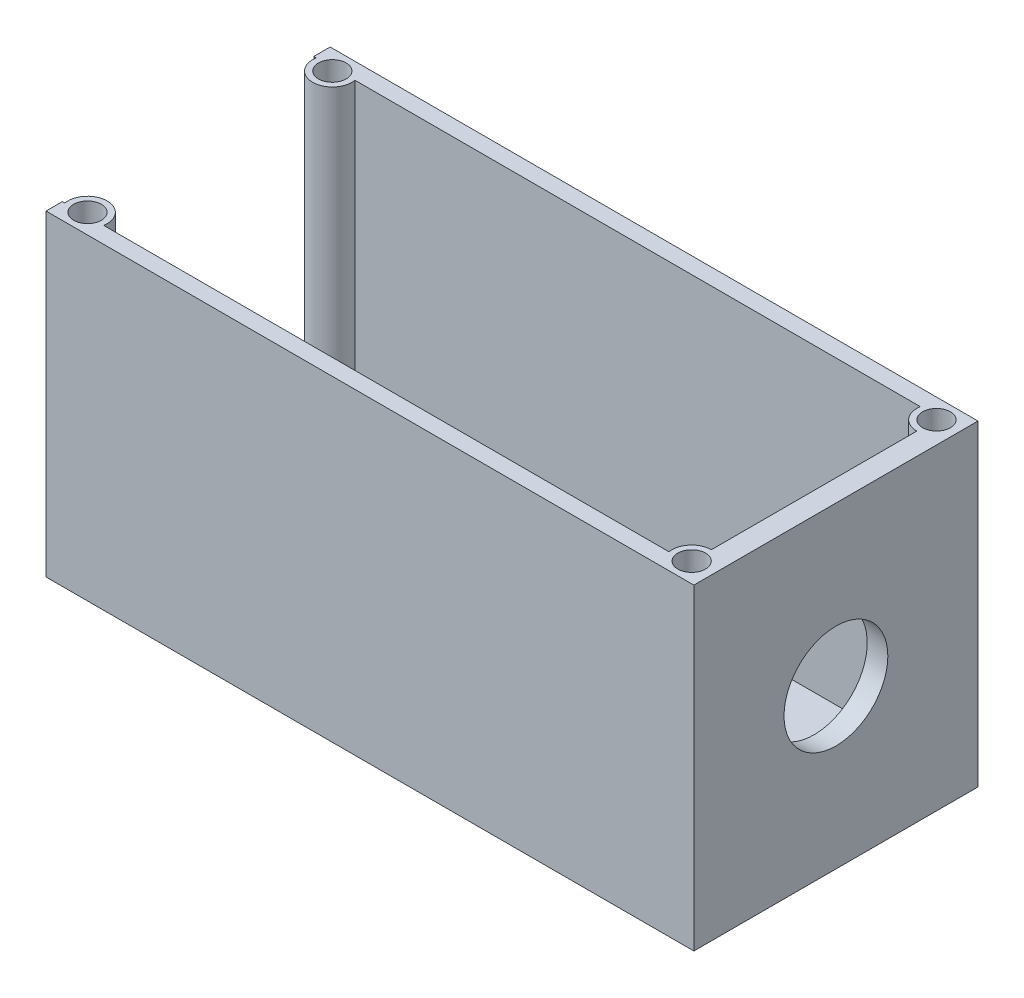
SolidWorks part; units mm, degrees
ref_plane "Front Plane" through (0, 0, 0) normal (0, 0, 1) x (1, 0, 0)
ref_plane "Top Plane" through (0, 0, 0) normal (0, 1, 0) x (1, 0, 0)
ref_plane "Right Plane" through (0, 0, 0) normal (1, 0, 0) x (0, 0, -1)
sketch "Sketch1" plane through (0, 0, 0) normal (0, 1, 0) x (1, 0, 0)
  line L1 (0, 0) -> (59.28, 0)
  line L2 (0, 0) -> (0, 26)
  line L3 (0, 26) -> (59.28, 26)
  line L4 (59.28, 0) -> (59.28, 26)
  dimension "D1" = 59.28
  dimension "D2" = 26
extrude "Boss-Extrude2" add sketch "Sketch1" along normal blind 29 contours L2 L3 L4 L1
sketch "Sketch3" plane through (0, 29, 0) normal (0, 1, 0) x (1, 0, 0)
  line L0 (0, 0) -> (0, 26) construction
  line L1 (57.28, 1.5) -> (0, 1.5)
  line L2 (57.28, 1.5) -> (57.28, 24.5)
  line L3 (57.28, 24.5) -> (0, 24.5)
  line L4 (0, 1.5) -> (0, 24.5)
  line L5 (0, 26) -> (59.28, 26) construction
  line L6 (0, 0) -> (59.28, 0) construction
  line L7 (59.28, 0) -> (59.28, 26) construction
  dimension "D1" = 1.5
  dimension "D2" = 1.5
  dimension "D3" = 2
extrude "Cut-Extrude1" cut sketch "Sketch3" against normal offset from surface (27.5 mm away) 1.5 up to face at (29.64, 0, -13)
sketch "Sketch4" plane through (59.28, 0, 0) normal (1, 0, 0) x (0, 0, -1)
  line L0 (0, 29) -> (26, 0) construction
  line L2 (26, 29) -> (0, 0) construction
  circle A0 centre (13, 14.5) radius 4.75
  point P6 (13, 14.5)
sketch "Sketch5" plane through (57.28, 0, 0) normal (-1, 0, 0) x (0, 0, 1)
  line L0 (-26, 29) -> (0, 0) construction
  line L2 (0, 29) -> (-26, 0) construction
  circle A0 centre (-13, 14.5) radius 4.8654
loft "Cut-Loft1" cut profiles "Sketch4", "Sketch5"
sketch "Sketch9" plane through (0, 29, 0) normal (0, 1, 0) x (1, 0, 0)
  line L0 (0, 0) -> (59.28, 0) construction
  line L2 (57.28, 1.5) -> (57.28, 24.5) construction
  circle A1 centre (57.28, 1.8) radius 1.8
  point P5 (0, 0)
extrude "Boss-Extrude4" add sketch "Sketch9" against normal up to surface (27.5 mm away) up to face at (28.64, 1.5, -13)
hole_wizard "Ø2.0mm Dowel Hole3" positions "Sketch12" profile "Sketch13" hole size "Ø2.0" standard "ANSI Metric"
sketch "Sketch12" plane through (0, 29, 0) normal (0, 1, 0) x (1, 0, 0)
  arc A0 (57.28, 3.6) -> (55.5052, 1.5) centre (57.28, 1.8) ccw construction
  point P0 (57.28, 1.8)
  dimension "D1" = 0
sketch "Sketch13" plane through (57.28, 29, -1.8) normal (1, 0, 0) x (0, 0, 1)
  line L0 (0, 0) -> (0, 10)
  line L1 (0, 10) -> (1.27, 10)
  line L2 (1.27, 10) -> (1.27, 0)
  line L5 (1.27, 0) -> (0, 0)
  line L10 (0, 10) -> (-1.27, 10) construction
  line L11 (0, -6.35) -> (0, 107.95) construction
  dimension "Hole Dia." = 2.54
  dimension "Hole Depth" = 10
  dimension "Drill Angle" = 180
ref_plane "Plane1" through (0, 0, -13) normal (0, 0, -1) x (-1, 0, 0)
mirror "Mirror1" about plane through (0, 0, -13) normal (0, 0, -1) of "Ø2.0mm Dowel Hole3", "Boss-Extrude4"
ref_plane "Plane2" through (29.64, 0, 0) normal (-1, 0, 0) x (0, 0, 1)
mirror "Mirror2" about plane through (29.64, 0, 0) normal (-1, 0, 0) of "Mirror1", "Boss-Extrude4", "Ø2.0mm Dowel Hole3"
